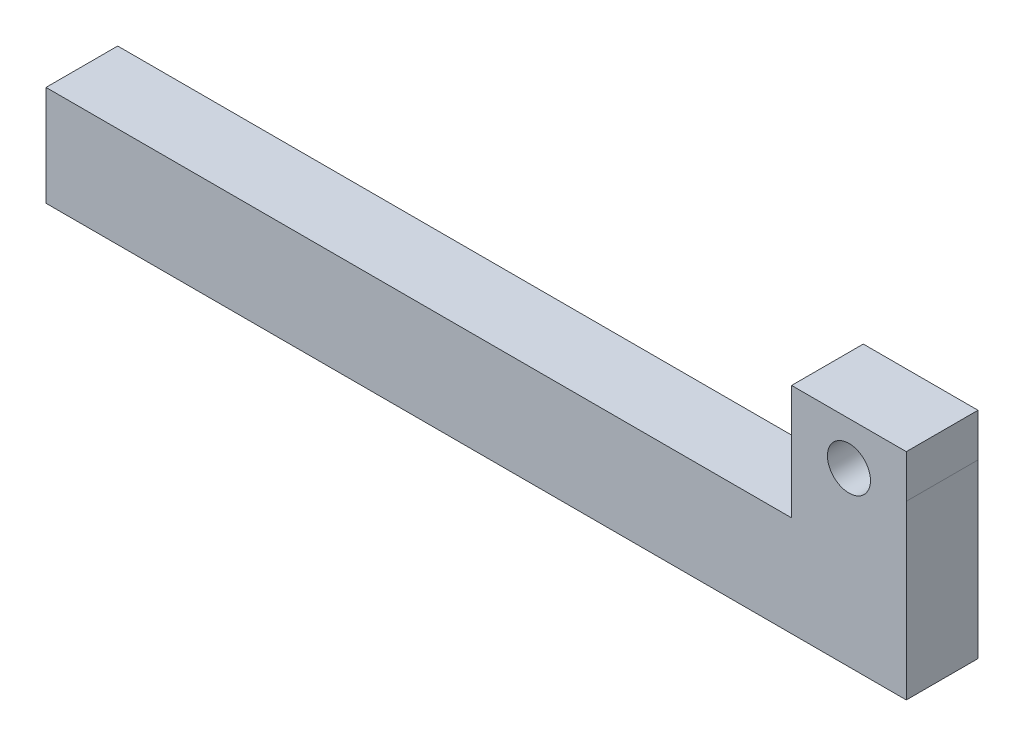
SolidWorks part; units mm, degrees
ref_plane "Front Plane" through (0, 0, 0) normal (0, 0, 1) x (1, 0, 0)
ref_plane "Top Plane" through (0, 0, 0) normal (0, 1, 0) x (1, 0, 0)
ref_plane "Right Plane" through (0, 0, 0) normal (1, 0, 0) x (0, 0, -1)
sketch "Sketch1" plane through (0, 0, 0) normal (0, 0, 1) x (1, 0, 0)
  line L0 (260, 35) -> (0, 35)
  line L1 (0, 0) -> (300, 0)
  line L2 (0, 0) -> (0, 35)
  line L6 (300, 0) -> (300, 75)
  line L7 (300, 75) -> (260, 75)
  line L8 (260, 35) -> (260, 75)
  circle A0 centre (280, 60) radius 7.5
  dimension "D7" = 15
  dimension "D1" = 35
  dimension "D2" = 300
  dimension "D3" = 40
  dimension "D4" = 75
  dimension "D5" = 20
  dimension "D6" = 60
extrude "Extrude1" add sketch "Sketch1" along normal blind 25
sketch "Sketch4" plane through (300, 0, 0) normal (1, 0, 0) x (0, 0, -1)
  line L0 (-25, 60) -> (0, 60)
  line L1 (-25, 0) -> (-25, 75) construction
  line L2 (0, 0) -> (0, 75) construction
  line L3 (-25, 0) -> (0, 0) construction
  dimension "D1" = 60
split line "Split Line3"
